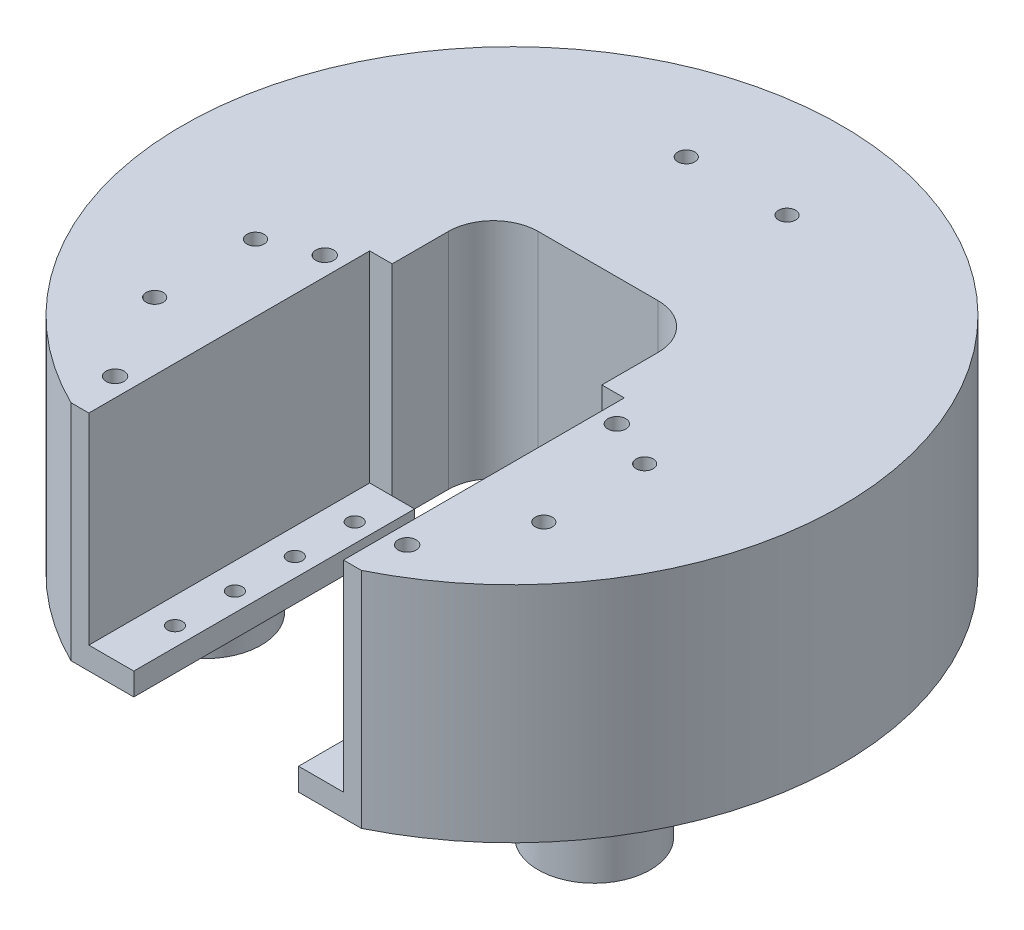
SolidWorks part; units mm, degrees
material "ABS"
ref_plane "Ön Düzlem" through (0, 0, 0) normal (0, 0, 1) x (1, 0, 0)
ref_plane "Üst Düzlem" through (0, 0, 0) normal (0, 1, 0) x (1, 0, 0)
ref_plane "Sağ Düzlem" through (0, 0, 0) normal (1, 0, 0) x (0, 0, -1)
sketch "Çizim2" plane through (0, 0, 0) normal (0, 1, 0) x (1, 0, 0)
  circle A0 centre (0, 0) radius 44
  dimension "D1" = 88
extrude "Yükseklik-Ekstrüzyon1" add sketch "Çizim2" along normal blind 48
sketch "Çizim3" plane through (0, 48, 0) normal (0, 1, 0) x (1, 0, 0)
  line L0 (-14, -2) -> (-17, -2)
  line L1 (-8, 11.5) -> (8, 11.5)
  line L2 (-17, -2) -> (-17, -39.5)
  line L3 (-17, -39.5) -> (17, -39.5)
  line L4 (17, -2) -> (17, -39.5)
  line L7 (-8, 11.5) -> (8, 11.5)
  line L8 (-14, 5.5) -> (-14, -2)
  line L9 (-14, -2) -> (14, -2)
  line L10 (14, 5.5) -> (14, -2)
  line L11 (-14, 11.5) -> (14, -2) construction
  line L12 (-14, -2) -> (14, 11.5) construction
  line L13 (14, -2) -> (17, -2)
  circle A0 centre (0, 0) radius 11
  arc A1 (14, 5.5) -> (8, 11.5) centre (8, 5.5) ccw
  arc A2 (-8, 11.5) -> (-14, 5.5) centre (-8, 5.5) ccw
  point P3 (0, -13.5)
  point P9 (0, 4.75)
  dimension "D1" = 22
  dimension "D9" = 6
  dimension "D2" = 34
  dimension "D3" = 37.5
  dimension "D4" = 11.5
  dimension "D5" = 13.5
  dimension "D6" = 28
  dimension "D7" = 11.5
  dimension "D8" = 3
extrude "Kes-Ekstrüzyon1" cut sketch "Çizim3" against normal blind 35 contours A0 L9 L0 L2 L3 L4 L13 | L1 A2 L8 L9 A0 L10 A1 | L9 A0 | L9 A0
sketch "Çizim5" plane through (0, 13, 0) normal (0, 1, 0) x (1, 0, 0)
  line L0 (-17, -39.5) -> (17, -39.5) construction
  line L1 (-10, -13.1) -> (10, -13.1)
  line L2 (-10, -13.1) -> (-10, -19.6)
  line L3 (-10, -19.6) -> (10, -19.6)
  line L4 (10, -13.1) -> (10, -19.6)
  line L5 (-10, -13.1) -> (10, -19.6) construction
  line L6 (-10, -19.6) -> (10, -13.1) construction
  line L7 (-17, -2) -> (-17, -39.5) construction
  line L8 (-11, -26.3) -> (-5, -26.3)
  line L9 (-11, -26.3) -> (-11, -33.5)
  line L10 (-11, -33.5) -> (-5, -33.5)
  line L11 (-5, -26.3) -> (-5, -33.5)
  line L12 (-11, -26.3) -> (-5, -33.5) construction
  line L13 (-11, -33.5) -> (-5, -26.3) construction
  line L14 (5, -26.3) -> (11, -26.3)
  line L15 (5, -26.3) -> (5, -33.5)
  line L16 (5, -33.5) -> (11, -33.5)
  line L17 (11, -26.3) -> (11, -33.5)
  line L18 (5, -26.3) -> (11, -33.5) construction
  line L19 (5, -33.5) -> (11, -26.3) construction
  line L20 (17, -2) -> (17, -39.5) construction
  circle A0 centre (0, 0) radius 5.5
  point P3 (0, -16.35)
  point P8 (8, -29.9)
  point P11 (-8, -29.9)
  dimension "D1" = 11
  dimension "D2" = 20
  dimension "D3" = 6.5
  dimension "D4" = 26.4
  dimension "D5" = 6
  dimension "D6" = 7.2
  dimension "D7" = 6
  dimension "D8" = 7.2
  dimension "D9" = 6
  dimension "D10" = 6
  dimension "D11" = 6
extrude "Servo Motor Boşluğu" cut sketch "Çizim5" against normal up to next
sketch "Çizim6" plane through (0, 48, 0) normal (0, 1, 0) x (1, 0, 0)
  line L1 (-60, -39.5) -> (60, -39.5)
  line L2 (-60, -39.5) -> (-60, -64.5)
  line L3 (-60, -64.5) -> (60, -64.5)
  line L4 (60, -39.5) -> (60, -64.5)
  dimension "D1" = 120
  dimension "D2" = 25
  dimension "D3" = 60
  dimension "D4" = 39.5
extrude "Kes-Ekstrüzyon3" cut sketch "Çizim6" against normal through all
sketch "Çizim7" plane through (0, 0, 39.5) normal (0, 0, 1) x (1, 0, 0)
  line L0 (19.3843, 0) -> (-19.3843, 0) construction
  line L1 (17, 0) -> (-17, 0)
  line L2 (17, 0) -> (17, 10)
  line L3 (17, 10) -> (-17, 10)
  line L4 (-17, 0) -> (-17, 10)
  dimension "D1" = 34
  dimension "D2" = 10
  dimension "D3" = 17
extrude "Kes-Ekstrüzyon4" cut sketch "Çizim7" against normal blind 37.5
sketch "Çizim8" plane through (0, 13, 0) normal (0, 1, 0) x (1, 0, 0)
  line L0 (-17, -2) -> (-17, -39.5) construction
  line L1 (-11, -2) -> (11, -2)
  line L2 (-11, -2) -> (-11, -39.5)
  line L3 (-11, -39.5) -> (11, -39.5)
  line L4 (11, -2) -> (11, -39.5)
  line L5 (-11, -2) -> (11, -39.5) construction
  line L6 (-11, -39.5) -> (11, -2) construction
  line L7 (17, -2) -> (17, -39.5) construction
  line L8 (-17, -2) -> (-14, -2) construction
  line L9 (-17, -39.5) -> (17, -39.5) construction
  line L10 (-11, -2) -> (-14, -2)
  line L11 (-14, -2) -> (-14, 6.5)
  line L12 (-8, 12.5) -> (8, 12.5)
  line L13 (14, 6.5) -> (14, -2)
  line L14 (14, -2) -> (11, -2)
  line L15 (-17, -2) -> (-17, -39.5) construction
  arc A0 (14, 6.5) -> (8, 12.5) centre (8, 6.5) ccw
  arc A1 (-8, 12.5) -> (-14, 6.5) centre (-8, 6.5) ccw
  point P0 (0, -20.75)
  point P23 (-14, 12.5)
  point P24 (-13.5, -7.5)
  point P25 (-13.5, -15.5)
  point P26 (-13.5, -23.5)
  point P27 (-13.5, -31.5)
  point P28 (13.5, -7.5)
  point P29 (13.5, -15.5)
  point P30 (13.5, -23.5)
  point P31 (13.5, -31.5)
  circle M10 centre (0, 0) radius 5.5
  line M12 (11, -33.5) -> (5, -33.5)
  line M13 (5, -33.5) -> (5, -26.3)
  line M14 (5, -26.3) -> (11, -26.3)
  line M15 (-5, -26.3) -> (-5, -33.5)
  line M16 (-5, -33.5) -> (-11, -33.5)
  line M18 (-11, -26.3) -> (-5, -26.3)
  line M19 (10, -13.1) -> (10, -19.6)
  line M20 (10, -19.6) -> (-10, -19.6)
  line M21 (-10, -19.6) -> (-10, -13.1)
  line M22 (-10, -13.1) -> (10, -13.1)
  line M23 (-14, 5.5) -> (-14, -2)
  line M26 (-17, -39.5) -> (17, -39.5)
  line M29 (14, -2) -> (14, 5.5)
  arc M30 (14, 5.5) -> (8, 11.5) centre (8, 5.5) ccw
  line M31 (8, 11.5) -> (-8, 11.5)
  arc M32 (-8, 11.5) -> (-14, 5.5) centre (-8, 5.5) ccw
  dimension "D4" = 6
  dimension "D1" = 6
  dimension "D2" = 6
  dimension "D3" = 14.5
  dimension "D5" = 3.5
  dimension "D6" = 5.5
  dimension "D7" = 8
  dimension "D8" = 8
  dimension "D9" = 8
  dimension "D10" = 3.5
extrude "Kes-Ekstrüzyon5" cut sketch "Çizim8" against normal through all contours L14 L10 L1 M29 M30 M31 M32 M23 M10 | L4 L1 L2 M10 M18 M15 M16 M26 M12 M13 M14 M22 M19 M20 M21 | L1 M10 | L1 M10
sketch "Vida Ref." plane through (0, 10, 0) normal (0, -1, 0) x (1, 0, 0)
  point P0 (-13.5, 31.5)
  point P1 (-13.5, 23.5)
  point P3 (-13.5, 15.5)
  point P5 (-13.5, 7.5)
  point P7 (13.5, 31.5)
  point P9 (13.5, 23.5)
  point P11 (13.5, 15.5)
  point P13 (13.5, 7.5)
hole_wizard "M2 Düz Başlı Makine Vidası İçin Havşa1" positions "3B Çizim1" profile "Çizim10" countersink size "M2" standard "ANSI Metrik" end condition up to next
sketch3d "3B Çizim1"
  point P0 (-13.5, 10, 31.5)
  point P3 (-13.5, 10, 23.5)
  point P6 (-13.5, 10, 15.5)
  point P9 (-13.5, 10, 7.5)
  point P12 (13.5, 10, 31.5)
  point P15 (13.5, 10, 23.5)
  point P18 (13.5, 10, 15.5)
  point P21 (13.5, 10, 7.5)
sketch "Çizim10" plane through (-13.5, 10, 31.5) normal (1, 0, 0) x (0, 0, -1)
  line L0 (0, 0) -> (0, 3)
  line L1 (0, 3) -> (1, 3)
  line L2 (1, 3) -> (1, 0.3)
  line L3 (1, 0.3) -> (1.3, 0)
  line L5 (1.3, 0) -> (0, 0)
  line L6 (-1, 0.3) -> (-1.3, 0) construction
  line L11 (0, -6.35) -> (0, 107.95) construction
  dimension "Thru Hole Dia." = 2
  dimension "Thru Hole Depth" = 3
  dimension "Near C'Sink Dia." = 2.6
  dimension "Near C'Sink Angle" = 90
sketch "Çizim11" plane through (0, 48, 0) normal (0, 1, 0) x (1, 0, 0)
  circle A0 centre (0, 0) radius 47.5
  dimension "D1" = 95
extrude "Kes-Ekstrüzyon6" cut sketch "Çizim11" against normal blind 8.16
sketch "Çizim13" plane through (0, 0, 0) normal (0, -1, 0) x (1, 0, 0)
  circle A0 centre (0, -30) radius 7.5
  dimension "D1" = 15
  dimension "D2" = 30
sketch "Çizim14" plane through (0, 0, 0) normal (0, -1, 0) x (1, 0, 0)
  circle A0 centre (0, 0) radius 47.5
  dimension "D1" = 95
extrude "Kes-Ekstrüzyon7" cut sketch "Çizim14" against normal blind 10
extrude "Taban Ayakları" add sketch "Çizim13" against normal blind 10
pattern_circular "Dairesel Kaplama1" count 3 over 360 about axis through (0, 0, 0) along (0, 1, 0) of "Taban Ayakları"
sketch "Sarhoş Tekerlek Konumu" plane through (0, 39.84, 0) normal (0, 1, 0) x (1, 0, 0)
  circle A0 centre (-25.9808, -15) radius 7.5
  circle A1 centre (25.9808, -15) radius 7.5
  circle A2 centre (0, 30) radius 7.5
  point P9 (-6.731, 30)
  point P10 (6.731, 30)
  point P11 (-25.9808, -8.269)
  point P12 (-25.9808, -21.731)
  point P13 (25.9808, -8.269)
  point P14 (25.9808, -21.731)
  dimension "D1" = 15
  dimension "D2" = 15
  dimension "D3" = 15
  dimension "D4" = 13.462
  dimension "D5" = 6.731
  dimension "D6" = 13.462
  dimension "D7" = 6.731
hole_wizard "3/8 Zıvana İçin Boru Zıvana Matkabı1" positions "3B Çizim2" profile "Çizim17" hole size "3/8" standard "ANSI İnç"
sketch3d "3B Çizim2"
  point P0 (-6.731, 39.84, -30)
  point P3 (6.731, 39.84, -30)
  point P6 (-25.9808, 39.84, 8.269)
  point P9 (-25.9808, 39.84, 21.731)
  point P12 (25.9808, 39.84, 8.269)
  point P15 (25.9808, 39.84, 21.731)
sketch "Çizim17" plane through (-6.731, 39.84, -30) normal (1, 0, 0) x (0, 0, 1)
  line L0 (0, 0) -> (0, 10)
  line L1 (0, 10) -> (1.143, 10)
  line L2 (1.143, 10) -> (1.143, 0)
  line L5 (1.143, 0) -> (0, 0)
  line L10 (0, 10) -> (-1.143, 10) construction
  line L11 (0, -6.35) -> (0, 107.95) construction
  dimension "Hole Dia." = 2.286
  dimension "Hole Depth" = 10
  dimension "Drill Angle" = 180
sketch "Çizim18" plane through (0, 39.84, 0) normal (0, 1, 0) x (1, 0, 0)
  line L0 (-17, -39.5) -> (-17, -2) construction
  line L1 (-19.3843, -39.5) -> (-17, -39.5) construction
  line L2 (17, -39.5) -> (17, -2) construction
  circle A0 centre (-19.5, -5.5) radius 1.2
  circle A1 centre (-19.5, -33.5) radius 1.2
  circle A2 centre (19.5, -5.5) radius 1.2
  circle A3 centre (19.5, -33.5) radius 1.2
  point P0 (-19.5, -33.5)
  point P1 (-19.5, -5.5)
  point P2 (19.5, -33.5)
  point P3 (19.5, -5.5)
  dimension "D5" = 2.4
  dimension "D1" = 2.5
  dimension "D2" = 6
  dimension "D3" = 34
  dimension "D4" = 2.5
extrude "Kes-Ekstrüzyon8" cut sketch "Çizim18" against normal blind 10
